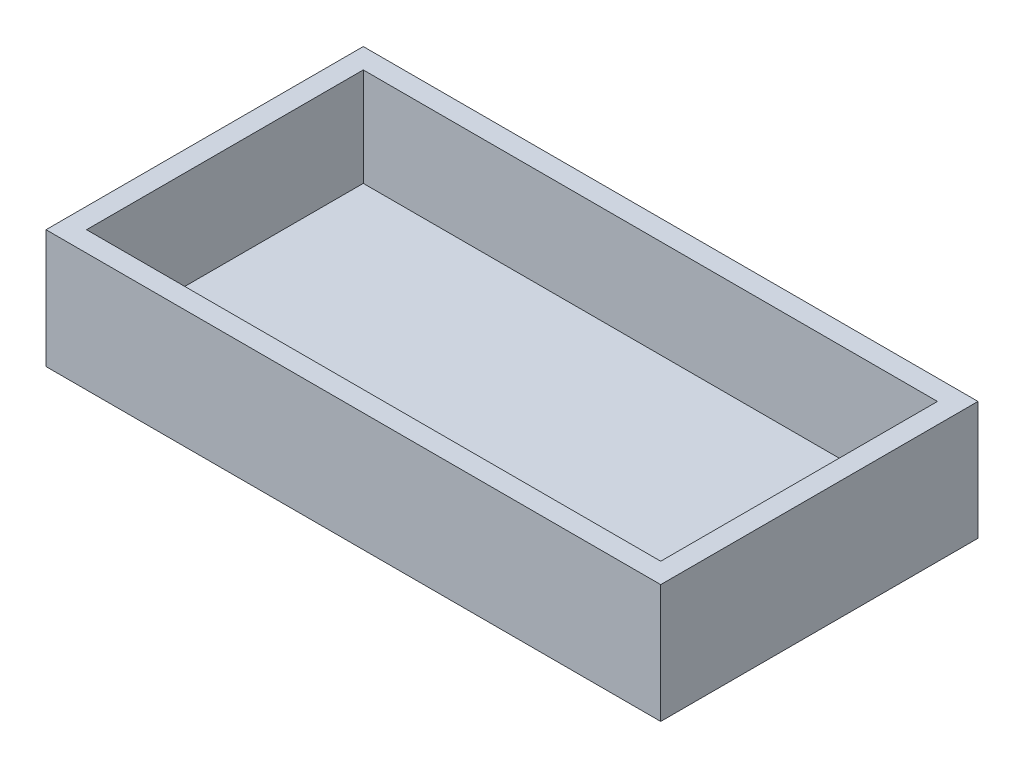
SolidWorks part; units mm, degrees
ref_plane "Front Plane" through (0, 0, 0) normal (0, 0, 1) x (1, 0, 0)
ref_plane "Top Plane" through (0, 0, 0) normal (0, 1, 0) x (1, 0, 0)
ref_plane "Right Plane" through (0, 0, 0) normal (1, 0, 0) x (0, 0, -1)
sketch "Sketch1" plane through (0, 0, 0) normal (0, 1, 0) x (1, 0, 0)
  line L1 (0, 0) -> (77.0636, 0)
  line L2 (0, 0) -> (0, 39.7764)
  line L3 (0, 39.7764) -> (77.0636, 39.7764)
  line L4 (77.0636, 0) -> (77.0636, 39.7764)
  dimension "D1" = 39.7764
  dimension "D2" = 77.0636
extrude "Boss-Extrude1" add sketch "Sketch1" along normal blind 14.859
shell "Shell1" thickness 2.54
